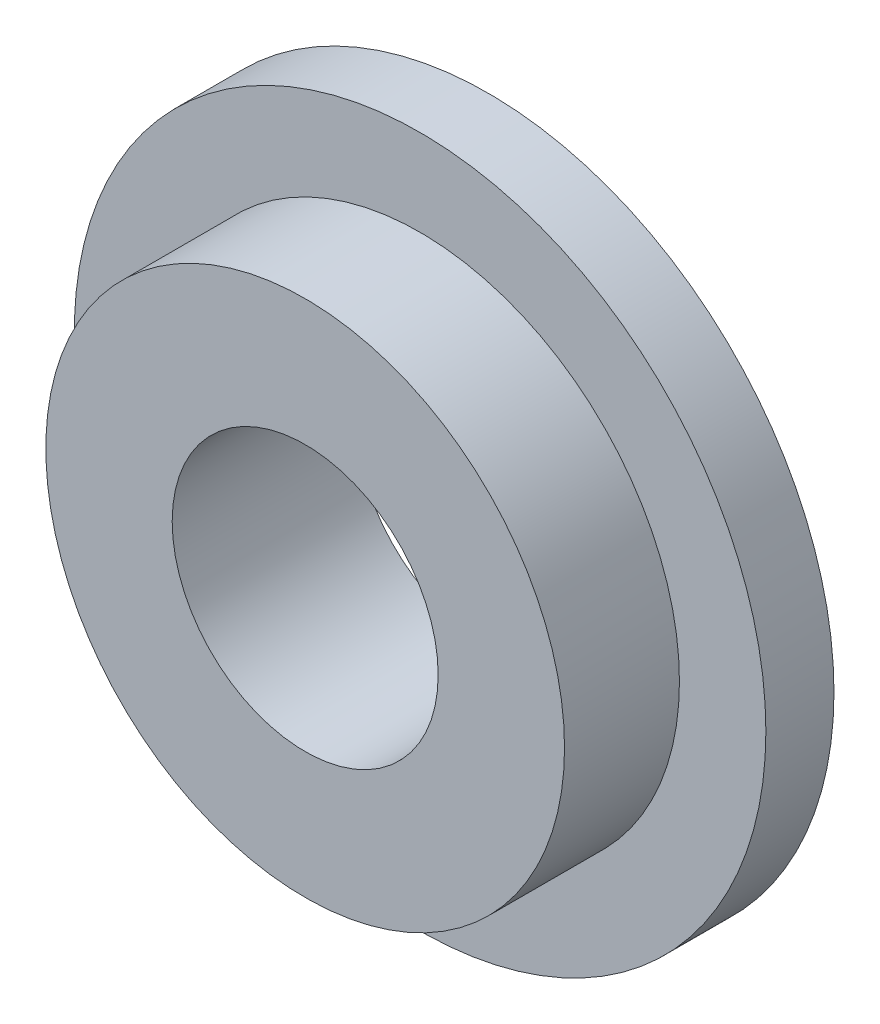
SolidWorks part; units mm, degrees
ref_plane "Front Plane" through (0, 0, 0) normal (0, 0, 1) x (1, 0, 0)
ref_plane "Top Plane" through (0, 0, 0) normal (0, 1, 0) x (1, 0, 0)
ref_plane "Right Plane" through (0, 0, 0) normal (1, 0, 0) x (0, 0, -1)
sketch "Sketch1" plane through (0, 0, 0) normal (0, 0, 1) x (1, 0, 0)
  circle A0 centre (0, 0) radius 20.6375
  circle A1 centre (0, 0) radius 7.9375
  dimension "D1" = 41.275
  dimension "D2" = 15.875
extrude "Boss-Extrude1" add sketch "Sketch1" along normal blind 4.064
sketch "Sketch2" plane through (0, 0, 4.064) normal (0, 0, 1) x (1, 0, 0)
  circle A0 centre (0, 0) radius 7.9375
  circle A1 centre (0, 0) radius 15.4788
extrude "Boss-Extrude2" add sketch "Sketch2" along normal blind 6.858
